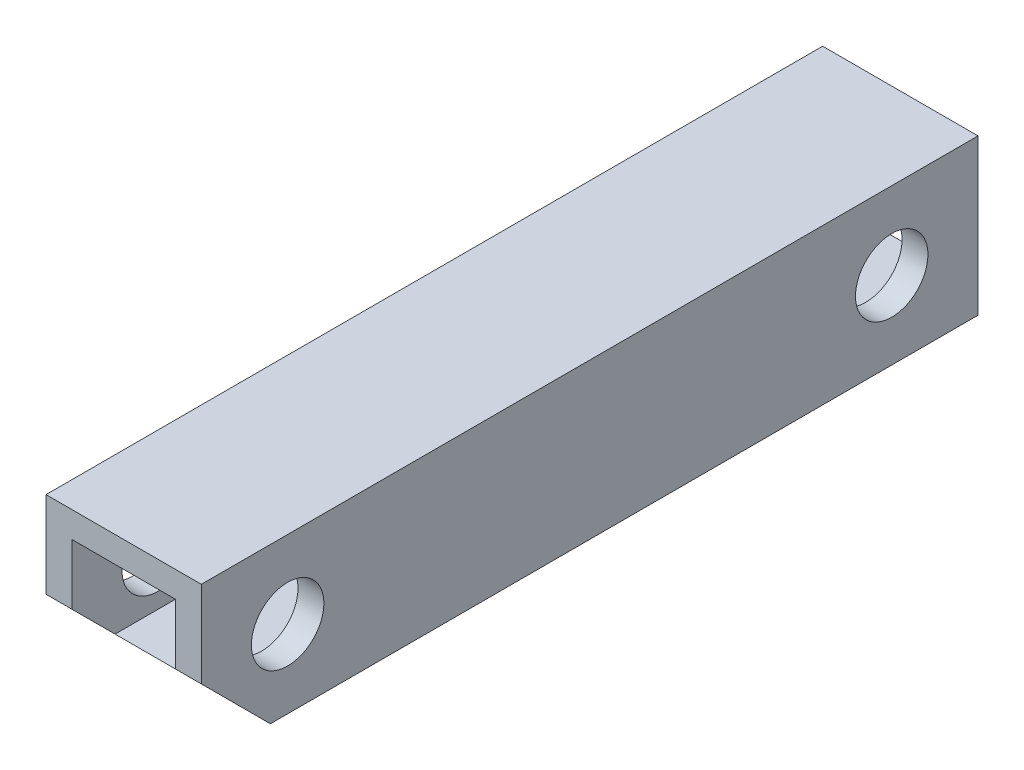
SolidWorks part; units mm, degrees
ref_plane "正面" through (0, 0, 0) normal (0, 0, 1) x (1, 0, 0)
ref_plane "平面" through (0, 0, 0) normal (0, 1, 0) x (1, 0, 0)
ref_plane "右側面" through (0, 0, 0) normal (1, 0, 0) x (0, 0, -1)
sketch "ｽｹｯﾁ1" plane through (0, 0, 0) normal (0, 0, 1) x (1, 0, 0)
  line L1 (-3, 3) -> (3, 3)
  line L2 (-3, 3) -> (-3, -3)
  line L3 (-3, -3) -> (3, -3)
  line L4 (3, 3) -> (3, -3)
  line L5 (-3, 3) -> (3, -3) construction
  line L6 (-3, -3) -> (3, 3) construction
  line L7 (-4.5, 4.5) -> (4.5, 4.5)
  line L8 (-4.5, 4.5) -> (-4.5, -4.5)
  line L9 (-4.5, -4.5) -> (4.5, -4.5)
  line L10 (4.5, 4.5) -> (4.5, -4.5)
  line L11 (-4.5, 4.5) -> (4.5, -4.5) construction
  line L12 (-4.5, -4.5) -> (4.5, 4.5) construction
  point P0 (0, 0)
  point P6 (0, 0)
  dimension "D1" = 6
  dimension "D2" = 6
  dimension "D3" = 9
extrude "ﾎﾞｽ - 押し出し1" add sketch "ｽｹｯﾁ1" along normal blind 45
sketch "ｽｹｯﾁ2" plane through (4.5, 0, 0) normal (1, 0, 0) x (0, 0, -1)
  line L0 (-45, 0) -> (-40, 0)
  line L1 (-45, -4.5) -> (-45, 4.5) construction
  line L2 (0, 0) -> (-5, 0)
  circle A0 centre (-40, 0) radius 2.1
  circle A1 centre (-5, 0) radius 2.1
  dimension "D3" = 4.2
  dimension "D4" = 4.2
  dimension "D1" = 5
  dimension "D2" = 5
extrude "ｶｯﾄ - 押し出し1" cut sketch "ｽｹｯﾁ2" against normal blind 30
sketch "ｽｹｯﾁ3" plane through (4.5, 0, 0) normal (1, 0, 0) x (0, 0, -1)
  line L5 (-45, -4.5) -> (-45, -0.5)
  line L6 (-45, -4.5) -> (-45, 4.5) construction
  line L7 (-45, -0.5) -> (-41, -4.5)
  line L8 (-45, -4.5) -> (0, -4.5) construction
  line L9 (-41, -4.5) -> (-45, -4.5)
  dimension "D1" = 4
  dimension "D2" = 4
extrude "ｶｯﾄ - 押し出し3" cut sketch "ｽｹｯﾁ3" against normal blind 10
